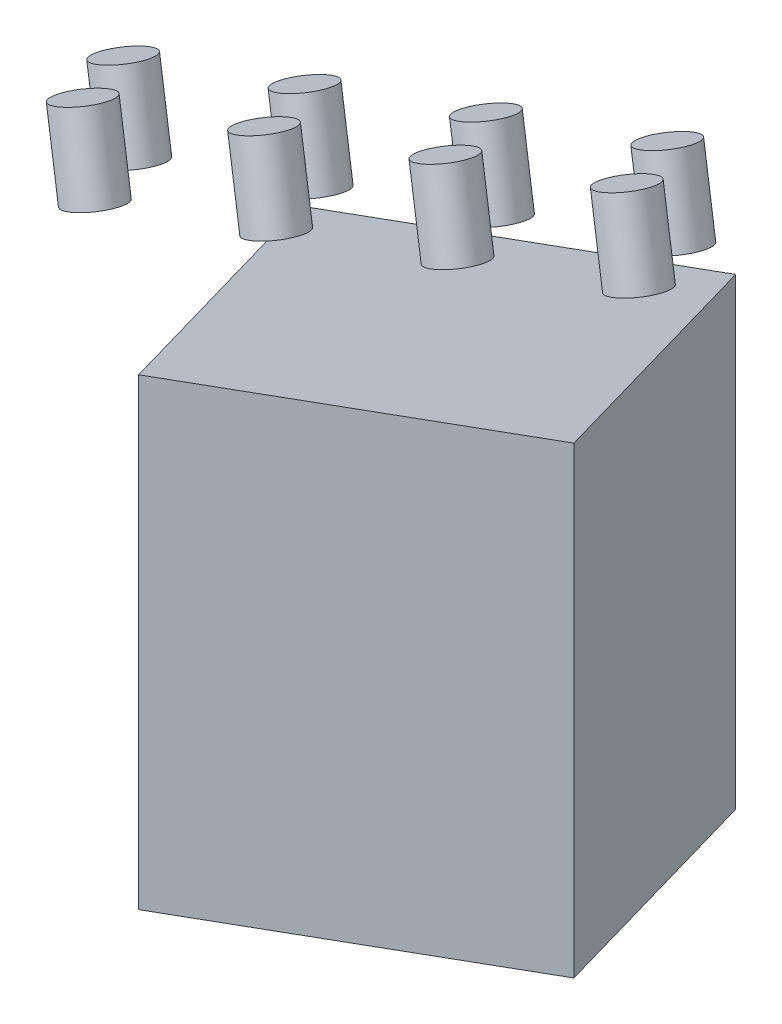
SolidWorks part; units mm, degrees
ref_plane "Ebene vorne" through (0, 0, 0) normal (0, 0, 1) x (1, 0, 0)
ref_plane "Ebene oben" through (0, 0, 0) normal (0, 1, 0) x (1, 0, 0)
ref_plane "Ebene rechts" through (0, 0, 0) normal (1, 0, 0) x (0, 0, -1)
sketch "SK Grundriss" plane through (0, 0, 0) normal (0, 0, 1) x (1, 0, 0)
  line L0 (0, 0) -> (0, 60)
  line L1 (0, 0) -> (56.3816, 20.5212)
  line L2 (0, 60) -> (56.3816, 80.5212)
  line L3 (56.3816, 20.5212) -> (56.3816, 80.5212)
  dimension "Winkel" = 70
  dimension "Seitenlänge" = 60
sketch "SK Schnittebene" plane through (0, 0, 0) normal (1, 0, 0) x (0, 0, -1)
  line L0 (0, 0) -> (-60, 0)
  dimension "D1" = 60
ref_plane "Ebene1" through (0, 0, 0) normal (-0.5736, 0.8192, 0) x (0, 0, 1)
sketch "SK Pfad" plane through (0, 0, 0) normal (-0.5736, 0.8192, 0) x (0, 0, 1)
  line L0 (0, 0) -> (60, 0) construction
  line L1 (0, 0) -> (49.1491, 34.4146)
  dimension "Länge egal" = 60
  dimension "Winkel" = 35
  dimension "Länge" = 60
sweep "Austragung1" add profiles "SK Grundriss" path "SK Pfad"
sketch "Skizze1" plane through (-18.6704, 51.2966, -9.8929) normal (-0.3365, 0.9246, -0.1783) x (0.9417, 0.3304, -0.0637)
  circle A0 centre (74.2954, -22.475) radius 3.3584
extrude "Aufsatz-Linear austragen1" add sketch "Skizze1" along normal blind 10 separate body
pattern_linear "Lineares Muster2" count 4 spacing 25 along (-0.9397, -0.342, 0) count 2 spacing 15 along (-0.4698, -0.329, -0.8192) of "Aufsatz-Linear austragen1"
equation "\"Anzahlx\"=4"
equation "\"D1@Lineares Muster2\"=\"Anzahlx\""
